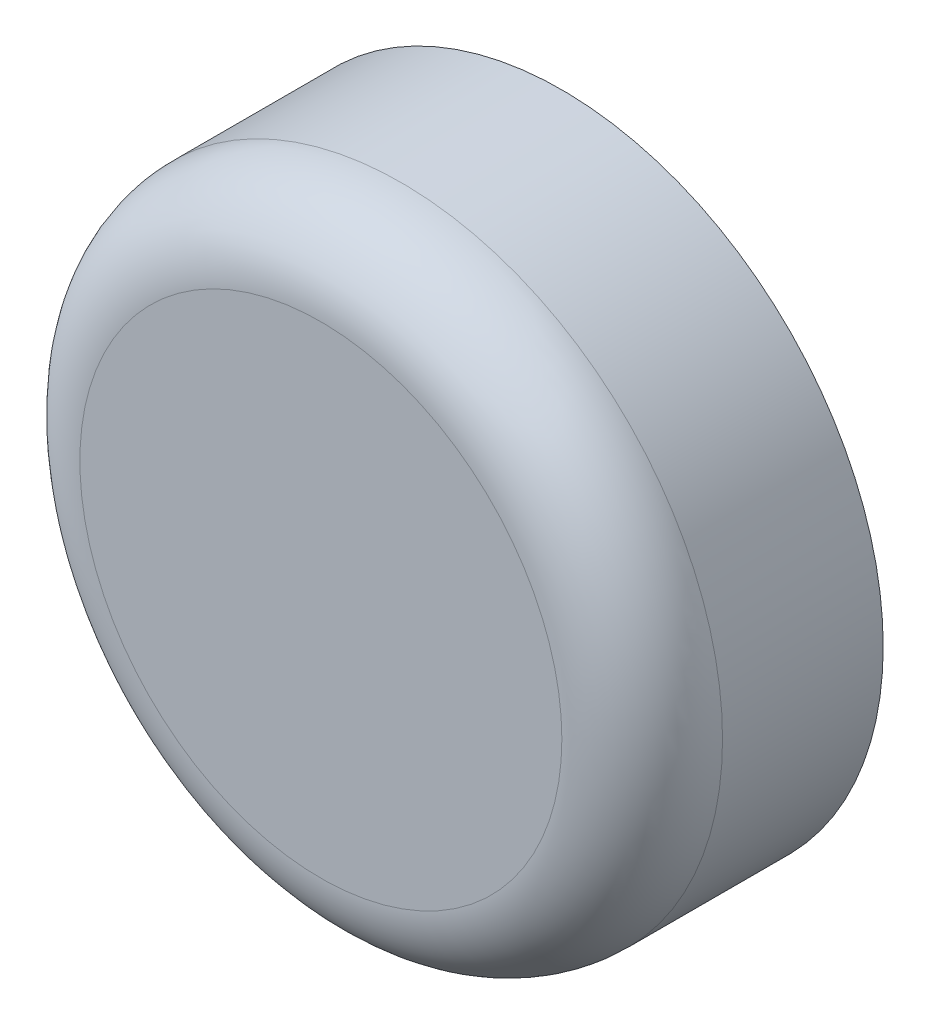
SolidWorks part; units mm, degrees
ref_plane "Ebene vorne" through (0, 0, 0) normal (0, 0, 1) x (1, 0, 0)
ref_plane "Ebene oben" through (0, 0, 0) normal (0, 1, 0) x (1, 0, 0)
ref_plane "Ebene rechts" through (0, 0, 0) normal (1, 0, 0) x (0, 0, -1)
sketch "Skizze1" plane through (0, 0, 0) normal (0, 0, 1) x (1, 0, 0)
  circle A0 centre (0, 0) radius 20
  dimension "D1" = 40
extrude "Aufsatz-Linear austragen1" add sketch "Skizze1" along normal blind 15
fillet "Verrundung1" radius 5 1 edges at (20, 0, 15)
sketch "Skizze2" plane through (0, 0, 0) normal (0, 0, -1) x (-1, 0, 0)
  line L1 (-5, -12.5) -> (5, -12.5)
  line L2 (-5, -12.5) -> (-5, 12.5)
  line L3 (-5, 12.5) -> (5, 12.5)
  line L4 (5, -12.5) -> (5, 12.5)
  line L5 (-5, -12.5) -> (5, 12.5) construction
  line L6 (-5, 12.5) -> (5, -12.5) construction
  point P0 (0, 0)
  dimension "D1" = 10
  dimension "D2" = 25
extrude "Schnitt-Linear austragen1" cut sketch "Skizze2" against normal blind 10
sketch "Skizze3" plane through (0, 0, 0) normal (0, 0, -1) x (-1, 0, 0)
  line L0 (0, -20) -> (0, 20) construction
  line L1 (-20, 0) -> (20, 0) construction
  circle A0 centre (0, 0) radius 20 construction
  circle A1 centre (13, 0) radius 1.25
  circle A2 centre (-13, 0) radius 1.25
  dimension "D1" = 2.5
  dimension "D2" = 13
extrude "Schnitt-Linear austragen2" cut sketch "Skizze3" against normal blind 5 contours A2 | A1
